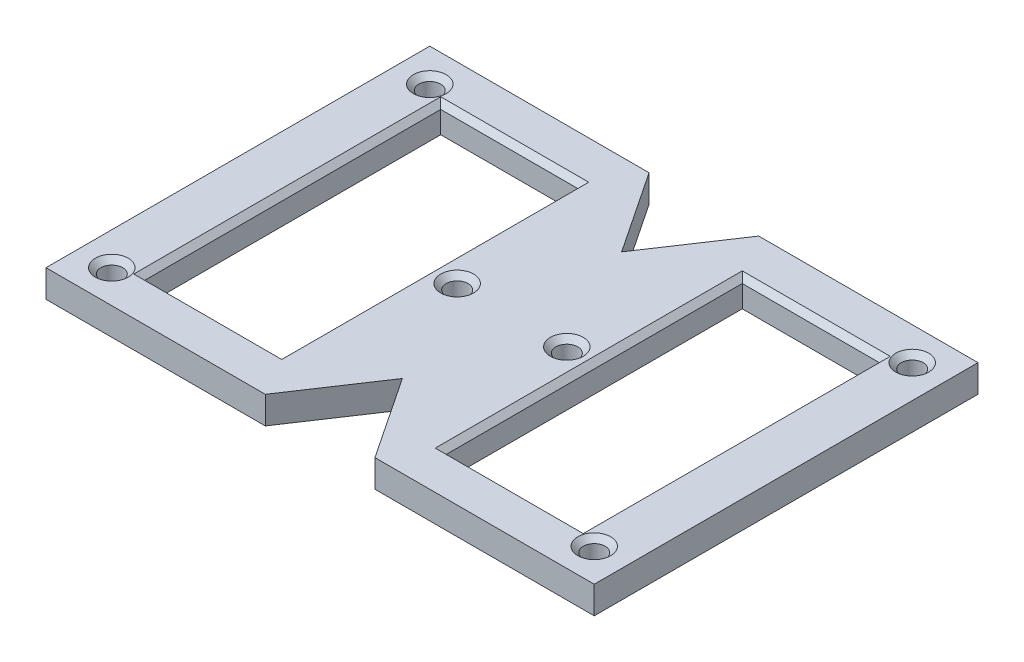
SolidWorks part; units mm, degrees
ref_plane "Alzado" through (0, 0, 0) normal (0, 0, 1) x (1, 0, 0)
ref_plane "Planta" through (0, 0, 0) normal (0, 1, 0) x (1, 0, 0)
ref_plane "Vista lateral" through (0, 0, 0) normal (1, 0, 0) x (0, 0, -1)
sketch "Croquis1" plane through (0, 0, 0) normal (0, 1, 0) x (1, 0, 0)
  line L1 (50, -35) -> (-50, -35)
  line L2 (50, -35) -> (50, 35)
  line L3 (50, 35) -> (-50, 35)
  line L4 (-50, -35) -> (-50, 35)
  line L5 (50, -35) -> (-50, 35) construction
  line L6 (50, 35) -> (-50, -35) construction
  point P0 (0, 0)
  dimension "D1" = 100
  dimension "D2" = 70
extrude "Saliente-Extruir1" add sketch "Croquis1" along normal blind 5
sketch "Croquis3" plane through (0, 5, 0) normal (0, 1, 0) x (1, 0, 0)
  line L0 (50, 35) -> (-50, 35) construction
  line L1 (-44, -29) -> (44, -29) construction
  line L2 (-44, -29) -> (-44, 29) construction
  line L3 (-44, 29) -> (44, 29) construction
  line L4 (44, -29) -> (44, 29) construction
  line L5 (-44, -29) -> (44, 29) construction
  line L6 (-44, 29) -> (44, -29) construction
  line L7 (-50, 35) -> (-50, -35) construction
  circle A0 centre (-44, 29) radius 2
  circle A1 centre (44, 29) radius 2
  circle A2 centre (44, -29) radius 2
  circle A3 centre (-44, -29) radius 2
  point P0 (0, 0)
  dimension "D1" = 4
  dimension "D2" = 6
  dimension "D3" = 6
extrude "Cortar-Extruir2" cut sketch "Croquis3" against normal through all
sketch "Croquis6" plane through (0, 5, 0) normal (0, 1, 0) x (1, 0, 0)
  line L0 (-10, 0) -> (10, 0) construction
  circle A0 centre (-10, 0) radius 2
  circle A1 centre (10, 0) radius 2
  circle A2 centre (-44, 29) radius 2 construction
  dimension "D1" = 10
  dimension "D2" = 10
extrude "Cortar-Extruir3" cut sketch "Croquis6" against normal through all
sketch "Croquis7" plane through (0, 0, 0) normal (0, -1, 0) x (1, 0, 0)
  line L1 (-40, -27) -> (-15, -27)
  line L2 (-40, -27) -> (-40, 27)
  line L3 (-40, 27) -> (-15, 27)
  line L4 (-15, -27) -> (-15, 27)
  line L5 (-40, -27) -> (-15, 27) construction
  line L6 (-40, 27) -> (-15, -27) construction
  line L10 (15, -27) -> (40, -27)
  line L11 (15, -27) -> (15, 27)
  line L12 (15, 27) -> (40, 27)
  line L13 (40, -27) -> (40, 27)
  line L14 (15, -27) -> (40, 27) construction
  line L15 (15, 27) -> (40, -27) construction
  point P0 (-27.5, 0)
  point P7 (27.5, 0)
  dimension "D1" = 15
  dimension "D2" = 15
  dimension "D3" = 40
  dimension "D4" = 40
  dimension "D5" = 27
  dimension "D6" = 27
extrude "Cortar-Extruir4" cut sketch "Croquis7" against normal through all
sketch "Croquis8" plane through (0, 5, 0) normal (0, 1, 0) x (1, 0, 0)
  line L0 (-10, 35) -> (0, 20)
  line L1 (50, 35) -> (-50, 35) construction
  line L2 (0, 20) -> (10, 35)
  line L4 (-10, 35) -> (10, 35)
  line L6 (-10, 0) -> (10, 0) construction
  point P4 (0, 35)
  point P14 (0, 0)
  dimension "D1" = 20
  dimension "D2" = 20
extrude "Cortar-Extruir5" cut sketch "Croquis8" against normal through all
mirror "Simetría1" about plane through (0, 0, 0) normal (0, 0, 1) of "Cortar-Extruir5"
chamfer "Chaflán1" distance 1 angle 45 14 edges at (44, 5, 31) (44, 5, -27) (10, 5, 2) (-10, 5, 2) (-44, 5, 31) (-44, 5, -27) (27.5, 5, 27) (40, 5, 0) (15, 5, 0) (27.5, 5, -27) (-27.5, 5, 27) (-15, 5, 0) (-27.5, 5, -27) (-40, 5, 0)
